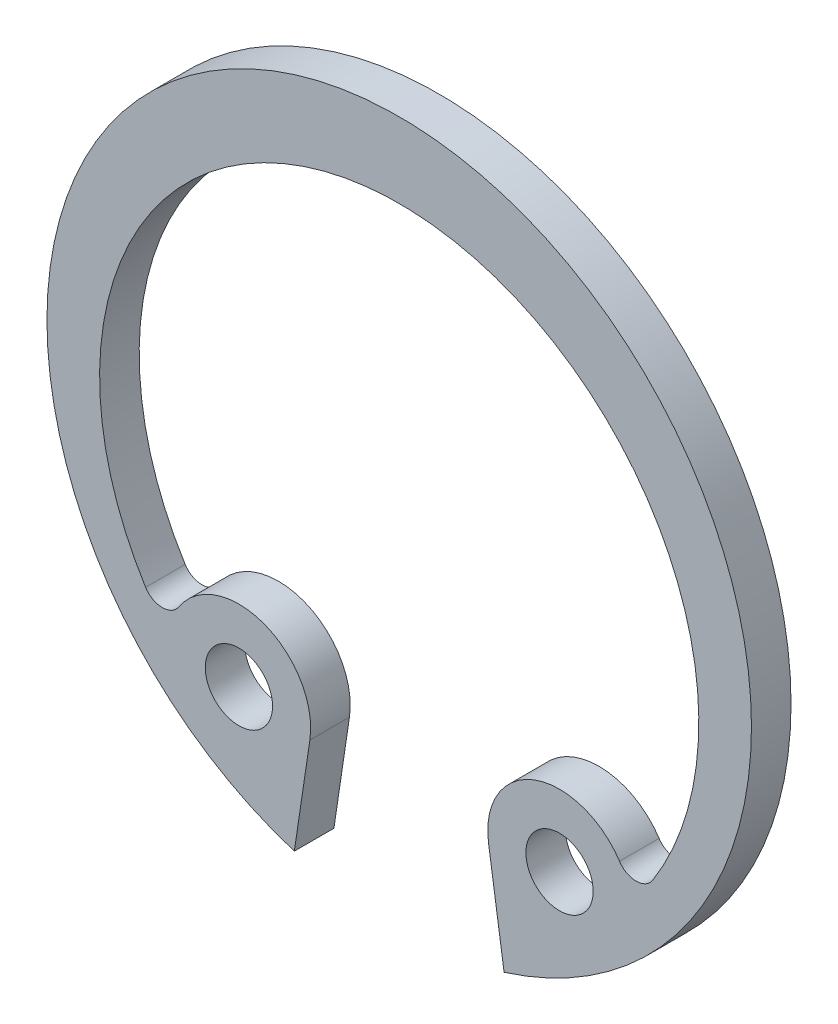
SolidWorks part; units mm, degrees
ref_plane "Front Plane" through (0, 0, 0) normal (0, 0, 1) x (1, 0, 0)
ref_plane "Top Plane" through (0, 0, 0) normal (0, 1, 0) x (1, 0, 0)
ref_plane "Right Plane" through (0, 0, 0) normal (1, 0, 0) x (0, 0, -1)
sketch "Sketch1" plane through (0, 0, 0) normal (0, 0, 1) x (1, 0, 0)
  line L0 (0, 0) -> (0, 8.9) construction
  line L1 (-2.2574, -5.8697) -> (-2.65, -8.4963)
  line L2 (2.2574, -5.8697) -> (2.65, -8.4963)
  line L3 (2.9881, -4.133) -> (5.2145, -7.2124) construction
  arc A0 (2.65, -8.4963) -> (-2.65, -8.4963) centre (0, 0) ccw
  arc A1 (-6.4076, -4.6008) -> (-5.5661, -4.6086) centre (-5.9844, -4.3346) ccw
  circle A2 centre (-4.05, -5.6018) radius 0.85
  circle A3 centre (4.05, -5.6018) radius 0.85
  circle A4 centre (0, 0) radius 4.5 construction
  arc A6 (-2.2574, -5.8697) -> (-5.5661, -4.6086) centre (-4.05, -5.6018) ccw
  arc A7 (5.5661, -4.6086) -> (2.2574, -5.8697) centre (4.05, -5.6018) ccw
  arc A8 (6.4076, -4.6008) -> (-6.4076, -4.6008) centre (0, -0.57) ccw
  arc A9 (6.4076, -4.6008) -> (5.5661, -4.6086) centre (5.9844, -4.3346) cw
  point P13 (0, 7)
  dimension "D1" = 0.5
  dimension "RIC_D2_s" = 17.8
  dimension "D2" = 17
  dimension "RIC_D4_s" = 15.14
  dimension "RIC_D0_s" = 1.7
  dimension "RIC_D5_s" = 9
  dimension "RIC_B_s" = 1.9
  dimension "RIC_MSM_2" = 8.1
  dimension "RIC_MSM_1" = 5.3
  dimension "RIC_A_s" = 3.8
extrude "Boss-Extrude1" add sketch "Sketch1" along normal blind 1
equation "\"RIC_D4_s@Sketch1\" = \"RIC_D2_s@Sketch1\" - 1.4 * \"RIC_B_s@Sketch1\""
